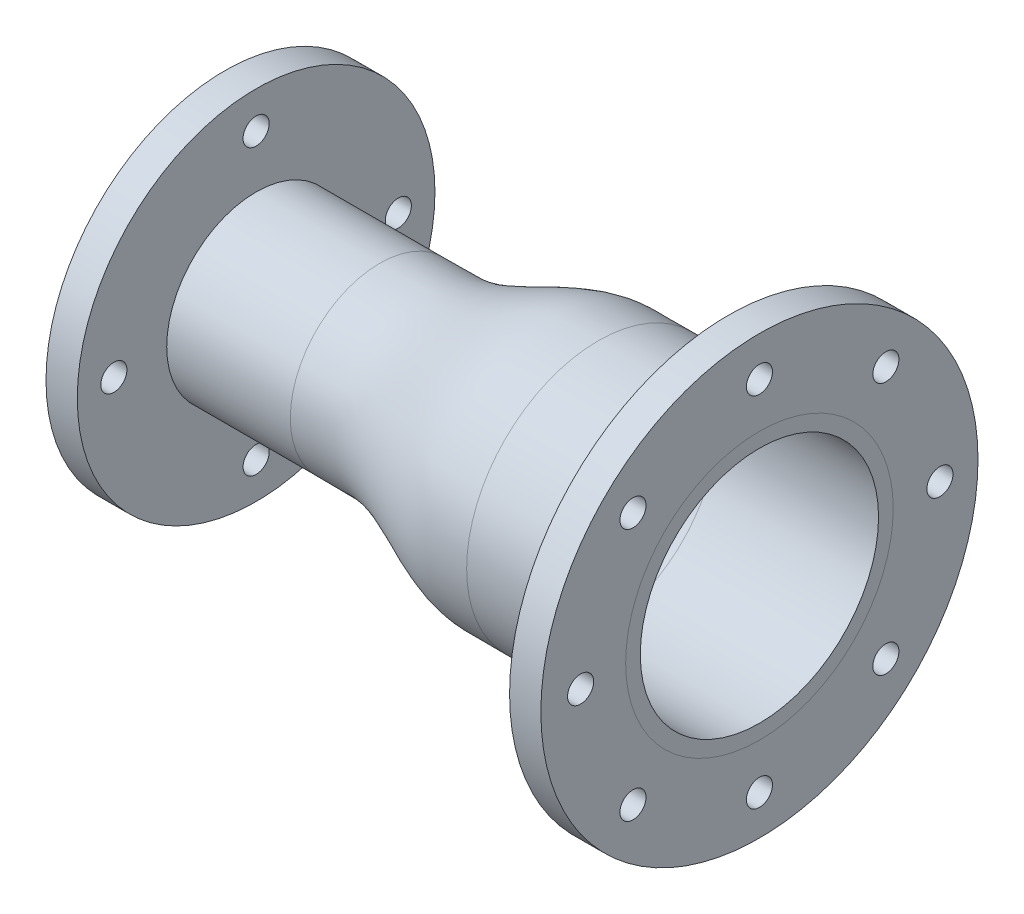
SolidWorks part; units mm, degrees
material "Cast Alloy Steel"
ref_plane "Front Plane" through (0, 0, 0) normal (0, 0, 1) x (1, 0, 0)
ref_plane "Top Plane" through (0, 0, 0) normal (0, 1, 0) x (1, 0, 0)
ref_plane "Right Plane" through (0, 0, 0) normal (1, 0, 0) x (0, 0, -1)
sketch "Sketch2" plane through (0, 0, 0) normal (0, 0, 1) x (1, 0, 0)
  line L0 (341.7, 0) -> (0, 0) construction
  line L4 (341.7, 76.1375) -> (341.7, 139.7)
  line L5 (20, 114.3) -> (0, 114.3)
  line L6 (341.7, 139.7) -> (321.7, 139.7)
  line L8 (0, 114.3) -> (0, 49.15)
  line L9 (321.7, 139.7) -> (321.7, 84.1375)
  line L10 (20, 114.3) -> (20, 57.15)
  line L11 (99, 57.15) -> (20, 57.15)
  line L12 (238.7, 76.1375) -> (321.7, 76.1375) construction
  line L13 (238.7, 84.1375) -> (321.7, 84.1375)
  line L14 (238.7, 76.1375) -> (341.7, 76.1375)
  line L15 (99, 49.15) -> (0, 49.15)
  line L16 (99, 49.15) -> (20, 49.15) construction
  spline S1 degree 3 poles (238.7, 84.1375) (238.3559, 84.1375) (237.6678, 84.1375) (236.4389, 84.1375) (234.866, 84.1375) (233.0965, 84.1375) (231.1795, 84.1375) (229.4099, 84.1375) (227.493, 84.1375) (225.7234, 84.1375) (223.8064, 84.1375) (222.0369, 84.1375) (220.1199, 84.1374) (218.3504, 84.1379) (216.4362, 84.1363) (214.6713, 84.1428) (212.7611, 84.0867) (210.998, 83.9819) (209.0881, 83.8116) (207.3251, 83.6037) (205.4153, 83.3256) (203.6525, 83.0215) (201.743, 82.6431) (199.9803, 82.2501) (198.071, 81.7796) (196.3085, 81.3056) (194.3993, 80.7519) (192.637, 80.2054) (190.7279, 79.5779) (188.9657, 78.9679) (187.0568, 78.2765) (185.2947, 77.6123) (183.3858, 76.8675) (181.6238, 76.159) (179.715, 75.3717) (177.9531, 74.629) (176.0443, 73.8103) (174.2824, 73.0438) (172.3737, 72.2052) (170.6119, 71.4256) (168.7018, 70.578) (166.9374, 69.795) (165.0248, 68.9495) (163.2593, 68.1744) (161.3467, 67.3439) (159.5811, 66.588) (157.6684, 65.784) (155.9029, 65.0579) (153.9901, 64.2918) (152.2245, 63.6059) (150.3116, 62.8888) (148.5459, 62.253) (146.6329, 61.5955) (144.8671, 61.0196) (142.954, 60.432) (141.188, 59.9252) (139.2748, 59.4172) (137.5086, 58.9881) (135.5952, 58.5689) (133.8288, 58.2258) (131.9153, 57.9039) (130.1487, 57.6544) (128.235, 57.4377) (126.4683, 57.2886) (124.7896, 57.1975) (123.4438, 57.157) (122.4205, 57.149) (121.678, 57.1501) (120.6018, 57.1498) (119.2022, 57.15) (117.2852, 57.15) (115.5156, 57.15) (113.5986, 57.15) (111.8291, 57.15) (109.9121, 57.15) (108.1426, 57.15) (106.2256, 57.15) (104.4561, 57.15) (102.5391, 57.15) (101.0399, 57.15) (99.811, 57.15) (99.2703, 57.15) (99, 57.15) knots 0 0 0 0 0.007154 0.014308 0.025551 0.039859 0.051101 0.06541 0.076652 0.09096 0.102202 0.116511 0.127753 0.142061 0.153304 0.167554 0.178755 0.193031 0.204272 0.218621 0.229935 0.244395 0.25581 0.270409 0.28194 0.296695 0.308353 0.323271 0.335057 0.350135 0.362043 0.377271 0.389288 0.404646 0.416757 0.43222 0.444402 0.459941 0.47217 0.487751 0.5 0.515621 0.527887 0.54348 0.555711 0.571243 0.583412 0.598851 0.610936 0.626254 0.638235 0.65341 0.665273 0.680292 0.692028 0.706883 0.718491 0.733185 0.74467 0.759216 0.770593 0.785014 0.796305 0.810635 0.821871 0.831257 0.838628 0.843146 0.846696 0.861005 0.872247 0.886555 0.897798 0.912106 0.923348 0.937657 0.948899 0.963207 0.974449 0.988758 0.994379 1 1 1 1 weights 0.576132 0.576132 0.576132 0.576132 0.576132 0.576132 0.576132 0.576132 0.576132 0.576132 0.576132 0.576132 0.576132 0.576132 0.576132 0.576132 0.576132 0.576132 0.576132 0.576132 0.576132 0.576132 0.576132 0.576132 0.576132 0.576132 0.576132 0.576132 0.576132 0.576132 0.576132 0.576132 0.576132 0.576132 0.576132 0.576132 0.576132 0.576132 0.576132 0.576132 0.576132 0.576132 0.576132 0.576132 0.576132 0.576132 0.576132 0.576132 0.576132 0.576132 0.576132 0.576132 0.576132 0.576132 0.576132 0.576132 0.576132 0.576132 0.576132 0.576132 0.576132 0.576132 0.576132 0.576132 0.576132 0.576132 0.576132 0.576132 0.576132 0.576132 0.576132 0.576132 0.576132 0.576132 0.576132 0.576132 0.576132 0.576132 0.576132 0.576132 0.576132 0.576132 0.576132
  spline S2 degree 1 poles (238.7, 76.1375) (99, 49.15) knots 0 0 1 1 construction
  spline S3 degree 3 poles (238.7, 76.1375) (235.6941, 76.1375) (231.1852, 76.1375) (225.925, 76.1375) (222.9189, 76.1376) (220.6647, 76.1373) (218.7847, 76.138) (217.2906, 76.1368) (216.1285, 76.1382) (215.0669, 76.1389) (213.7925, 76.1189) (211.4967, 76.0157) (208.2293, 75.6894) (204.2706, 75.0272) (200.2987, 74.1207) (194.9854, 72.6231) (188.3215, 70.2833) (180.2754, 66.9614) (172.1262, 63.3455) (163.7903, 59.6453) (155.1646, 56.0793) (147.6413, 53.4297) (141.3789, 51.6621) (136.5564, 50.5598) (131.6159, 49.7302) (127.4038, 49.3093) (124.4378, 49.1746) (122.9302, 49.1514) (122.1007, 49.1494) (121.357, 49.1504) (120.4173, 49.1498) (118.9131, 49.1501) (117.0359, 49.15) (114.7809, 49.15) (111.7752, 49.15) (106.5147, 49.15) (102.0059, 49.15) (99, 49.15) knots 0 0 0 0 0.0625 0.09375 0.109375 0.125 0.140625 0.148438 0.15625 0.164062 0.171875 0.1875 0.21875 0.25 0.28125 0.3125 0.375 0.4375 0.5 0.5625 0.625 0.6875 0.71875 0.75 0.78125 0.8125 0.828125 0.835938 0.839844 0.84375 0.851562 0.859375 0.875 0.890625 0.90625 0.9375 1 1 1 1
  dimension "D1" = 20
  dimension "D2" = 8
revolve "Revolve1" add sketch "Sketch2" angle 360 about L0
sketch "Sketch3" plane through (341.7, 0, 0) normal (1, 0, 0) x (0, 0, -1)
  circle A0 centre (0, -120.65) radius 11.175
  circle A1 centre (0, 0) radius 120.65 construction
  dimension "D1" = 22.35
  dimension "D2" = 241.3
extrude "Cut-Extrude1" [suppressed] cut sketch "Sketch3" against normal up to surface (20 mm away)
sketch "Sketch4" plane through (0, 0, 0) normal (-1, 0, 0) x (0, 0, 1)
  circle A0 centre (0, 0) radius 95.25 construction
  circle A1 centre (0, 95.25) radius 9.5
  dimension "D1" = 190.5
  dimension "D2" = 19
extrude "Cut-Extrude2" [suppressed] cut sketch "Sketch4" against normal up to surface (20 mm away)
pattern_circular "CirPattern1" [suppressed] count 4 over 360 about axis through (341.7, 0, 0) along (-1, 0, 0)
sketch "Sketch5" plane through (341.7, 0, 0) normal (1, 0, 0) x (0, 0, -1)
  circle A0 centre (0, 0) radius 85.5
  dimension "D1" = 171
split line "Split Line1"
hole_wizard "5/8 Clearance Hole1" positions "Sketch6" profile "Sketch7" hole size "5/8" standard "Ansi Inch"
sketch "Sketch6" plane through (0, -86.9453, 61.2299) normal (-1, 0, 0) x (0, 0, 1)
  line L0 (-61.2299, 86.9453) -> (160.2598, 86.9453) construction
  line L1 (-61.2299, 86.9453) -> (-61.2299, 296.6144) construction
  line L2 (-61.2299, 86.9453) -> (-291.9631, 86.9453) construction
  line L3 (-61.2299, 86.9453) -> (-61.2299, -121.1078) construction
  circle A0 centre (-61.2299, 86.9453) radius 90.9114 construction
  point P0 (-61.2299, 177.798)
  point P1 (29.6815, 86.9453)
  point P2 (-61.2299, -3.9661)
  point P3 (-152.1413, 86.9453)
sketch "Sketch7" plane through (0, 90.8528, 0) normal (0, 1, 0) x (0, 0, 1)
  line L0 (0, 0) -> (0, 20)
  line L1 (0, 20) -> (8.3337, 20)
  line L2 (8.3337, 20) -> (8.3337, 0)
  line L3 (8.3337, 0) -> (0, 0)
  line L4 (0, -6.35) -> (0, 107.95) construction
  dimension "Thru Hole Dia." = 16.6675
  dimension "Thru Hole Depth" = 20
hole_wizard "CSK for 5/8 Flat Head Machine Screw (100)1" positions "Sketch10" profile "Sketch11" countersink size "5/8" standard "Ansi Inch"
sketch "Sketch10" plane through (321.7, -86.9453, 61.2299) normal (-1, 0, 0) x (0, 0, 1)
  line L0 (-61.2299, 86.9453) -> (-61.2299, 353.2126) construction
  line L1 (-61.2299, 86.9453) -> (208.6165, 86.9453) construction
  line L2 (-61.2299, 86.9453) -> (-335.3638, 86.9453) construction
  line L3 (-61.2299, 86.9453) -> (-61.2299, -193.2291) construction
  line L7 (-61.2299, 86.9453) -> (113.4341, 261.6093) construction
  line L8 (-61.2299, 86.9453) -> (150.6399, -124.9245) construction
  line L9 (-61.2299, 86.9453) -> (-186.2909, 212.0063) construction
  line L10 (-61.2299, 86.9453) -> (-176.5965, -28.4213) construction
  circle A0 centre (-61.2299, 86.9453) radius 114.3 construction
  point P0 (-61.2299, 201.2453)
  point P1 (-176.5965, 86.9453)
  point P2 (-142.0522, 167.7676)
  point P3 (19.5924, 167.7676)
  point P4 (53.0701, 86.9453)
  point P5 (19.5924, 6.123)
  point P6 (-61.2299, -27.4065)
  point P7 (-142.0522, 6.123)
sketch "Sketch11" plane through (321.7, 114.3, 0) normal (0, 1, 0) x (0, 0, 1)
  line L0 (0, 0) -> (0, 20)
  line L1 (0, 20) -> (8.3337, 20)
  line L2 (8.3337, 20) -> (8.3337, 6.5623)
  line L3 (8.3337, 6.5623) -> (16.1544, 0)
  line L4 (16.1544, 0) -> (0, 0)
  line L5 (-8.3337, 6.5623) -> (-16.1544, 0) construction
  line L6 (0, -6.35) -> (0, 107.95) construction
  dimension "Thru Hole Dia." = 16.6675
  dimension "Thru Hole Depth" = 20
  dimension "Near C'Sink Dia." = 32.3088
  dimension "Near C'Sink Angle" = 100
hole_wizard "CSK for 5/8 Flat Head Machine Screw (100)2" [suppressed] positions "Sketch12" profile "Sketch13" countersink size "5/8" standard "Ansi Inch"
sketch "Sketch12" plane through (321.7, -86.9453, 61.2299) normal (-1, 0, 0) x (0, 0, 1)
  point P0 (-64.3378, 197.2771)
  point P1 (39.851, 49.4978)
  point P2 (-73.6499, -26.8437)
  point P3 (-171.7422, 70.605)
sketch "Sketch13" plane through (321.7, 110.3318, -3.1079) normal (0, 1, 0) x (0, 0, 1)
  line L0 (0, 0) -> (0, 20)
  line L1 (0, 20) -> (8.3337, 20)
  line L2 (8.3337, 20) -> (8.3337, 6.5623)
  line L3 (8.3337, 6.5623) -> (16.1544, 0)
  line L4 (16.1544, 0) -> (0, 0)
  line L5 (-8.3337, 6.5623) -> (-16.1544, 0) construction
  line L6 (0, -6.35) -> (0, 107.95) construction
  dimension "Thru Hole Dia." = 16.6675
  dimension "Thru Hole Depth" = 20
  dimension "Near C'Sink Dia." = 32.3088
  dimension "Near C'Sink Angle" = 100
